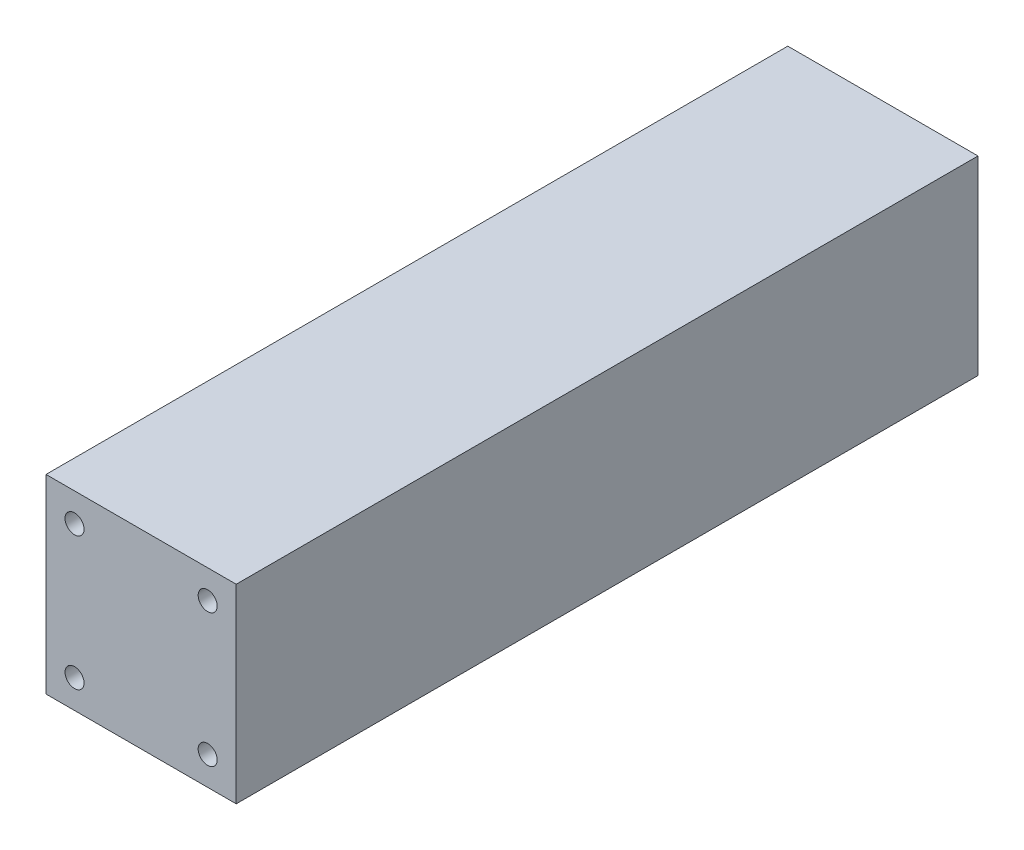
SolidWorks part; units mm, degrees
material "6061-T6 Al"
ref_plane "Front" through (0, 0, 0) normal (0, 0, 1) x (1, 0, 0)
ref_plane "Top" through (0, 0, 0) normal (0, 1, 0) x (1, 0, 0)
ref_plane "Right" through (0, 0, 0) normal (1, 0, 0) x (0, 0, -1)
sketch "Sketch1" plane through (0, 0, 0) normal (0, 0, 1) x (1, 0, 0)
  line L0 (0, 0) -> (0, 63.5) construction
  line L1 (-63.5, 63.5) -> (63.5, 63.5)
  line L2 (-63.5, 63.5) -> (-63.5, -63.5)
  line L3 (-63.5, -63.5) -> (63.5, -63.5)
  line L4 (63.5, 63.5) -> (63.5, -63.5)
  line L5 (0, 0) -> (-63.5, 0) construction
  dimension "D1" = 127
  dimension "D2" = 127
extrude "Boss-Extrude1" add sketch "Sketch1" along normal blind 495.3
hole_wizard "1/2-13 Tapped Hole1" positions "Sketch3" profile "Sketch2" tap size "1/2-13" standard "Ansi Inch"
sketch "Sketch3" plane through (0, 0, 495.3) normal (0, 0, 1) x (1, 0, 0)
  line L0 (-44.45, 44.45) -> (44.45, 44.45) construction
  line L1 (-44.45, 44.45) -> (-44.45, -44.45) construction
  line L2 (44.45, 44.45) -> (44.45, -44.45) construction
  line L3 (-44.45, -44.45) -> (44.45, -44.45) construction
  line L4 (0, 0) -> (0, 44.45) construction
  line L5 (0, 0) -> (44.45, 0) construction
  point P0 (44.45, 44.45)
  point P1 (44.45, -44.45)
  point P3 (-44.45, -44.45)
  point P5 (-44.45, 44.45)
  dimension "D1" = 88.9
sketch "Sketch2" plane through (44.45, 44.45, 495.3) normal (1, 0, 0) x (0, -1, 0)
  line L0 (0, 0) -> (0, 34.4869)
  line L1 (0, 34.4869) -> (5.3581, 31.2674)
  line L2 (5.3581, 31.2674) -> (5.3581, 25.4)
  line L3 (5.3581, 25.4) -> (6.35, 25.4)
  line L4 (6.35, 25.4) -> (6.35, 0)
  line L5 (6.35, 0) -> (0, 0)
  line L10 (0, 34.4869) -> (-5.3581, 31.2674) construction
  line L11 (0, -6.35) -> (0, 107.95) construction
  dimension "Tap Drill Dia." = 10.7163
  dimension "Tap Drill Depth" = 31.2674
  dimension "Thread Major Dia." = 12.7
  dimension "Thread Depth" = 25.4
  dimension "Drill Angle" = 118
hole_wizard "1/2-13 Tapped Hole2" positions "Sketch5" profile "Sketch4" tap size "1/2-13" standard "Ansi Inch"
sketch "Sketch5" plane through (0, 0, 0) normal (0, 0, -1) x (-1, 0, 0)
  point P1 (-44.45, 44.45)
  point P4 (44.45, 44.45)
  point P7 (-44.45, -44.45)
  point P10 (44.45, -44.45)
sketch "Sketch4" plane through (44.45, 44.45, 0) normal (1, 0, 0) x (0, 1, 0)
  line L0 (0, 0) -> (0, 34.4869)
  line L1 (0, 34.4869) -> (5.3581, 31.2674)
  line L2 (5.3581, 31.2674) -> (5.3581, 25.4)
  line L3 (5.3581, 25.4) -> (6.35, 25.4)
  line L4 (6.35, 25.4) -> (6.35, 0)
  line L5 (6.35, 0) -> (0, 0)
  line L10 (0, 34.4869) -> (-5.3581, 31.2674) construction
  line L11 (0, -6.35) -> (0, 107.95) construction
  dimension "Tap Drill Dia." = 10.7163
  dimension "Tap Drill Depth" = 31.2674
  dimension "Thread Major Dia." = 12.7
  dimension "Thread Depth" = 25.4
  dimension "Drill Angle" = 118
